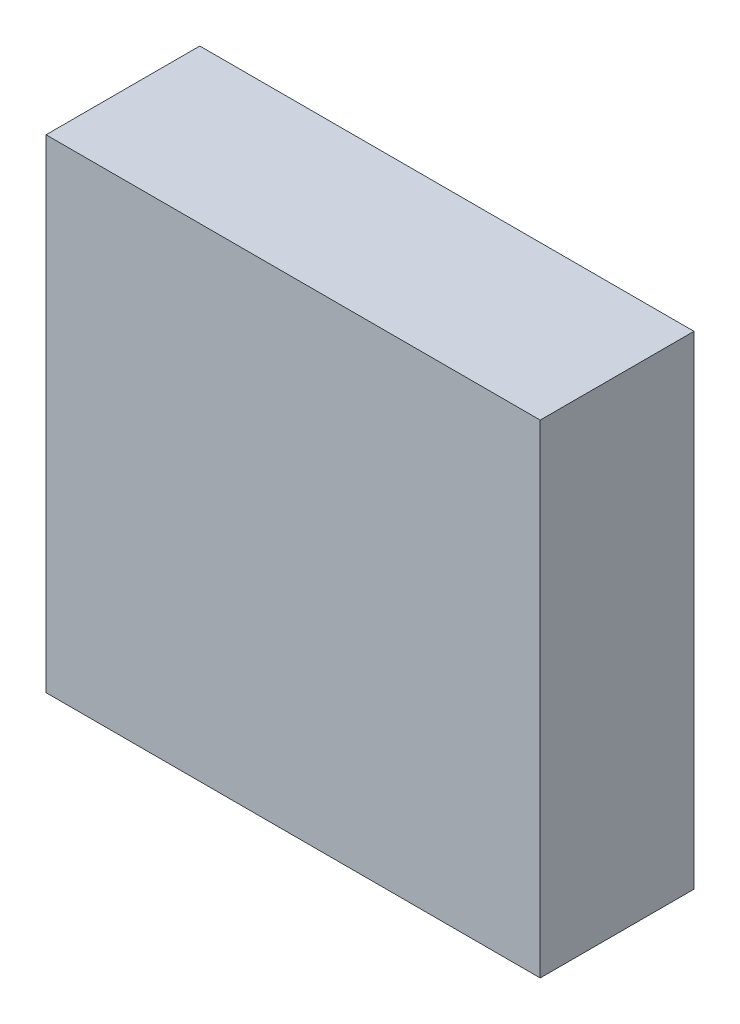
SolidWorks part; units mm, degrees
ref_plane "Front Plane" through (0, 0, 0) normal (0, 0, 1) x (1, 0, 0)
ref_plane "Top Plane" through (0, 0, 0) normal (0, 1, 0) x (1, 0, 0)
ref_plane "Right Plane" through (0, 0, 0) normal (1, 0, 0) x (0, 0, -1)
sketch "Sketch1" plane through (0, 0, 0) normal (0, 0, 1) x (1, 0, 0)
  line L0 (0, 0) -> (0, 129.6771) construction
  line L1 (0, 0) -> (185.4609, 0) construction
  line L3 (-57.15, 55.88) -> (57.15, 55.88)
  line L4 (-57.15, 55.88) -> (-57.15, -55.88)
  line L5 (-57.15, -55.88) -> (57.15, -55.88)
  line L6 (57.15, 55.88) -> (57.15, -55.88)
  point P8 (0, 0)
  point P9 (0, 0)
  dimension "D1" = 111.76
  dimension "D2" = 114.3
extrude "Boss-Extrude1" add sketch "Sketch1" along normal mid plane 35.56
